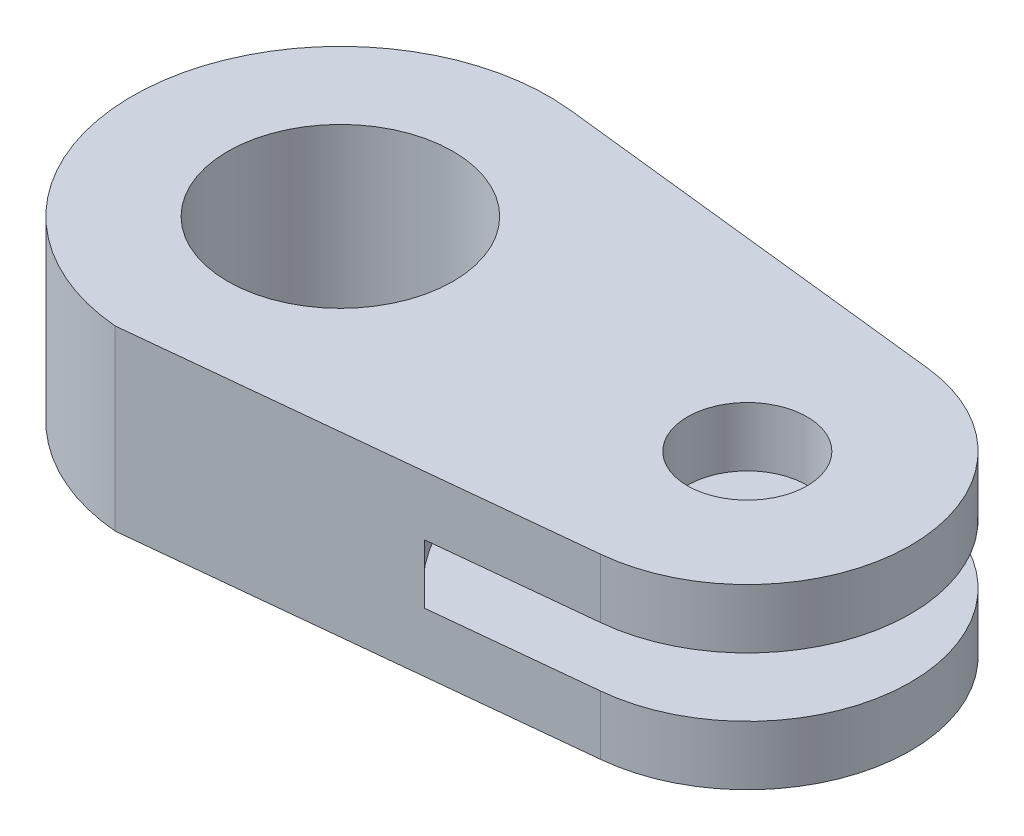
SolidWorks part; units mm, degrees
ref_plane "Front Plane" through (0, 0, 0) normal (0, 0, 1) x (1, 0, 0)
ref_plane "Top Plane" through (0, 0, 0) normal (0, 1, 0) x (1, 0, 0)
ref_plane "Right Plane" through (0, 0, 0) normal (1, 0, 0) x (0, 0, -1)
sketch "Эскиз1" plane through (0, 0, 0) normal (0, 1, 0) x (1, 0, 0)
  line L0 (6.2273, 55.9019) -> (114.7926, 43.8081)
  line L1 (-4.7951, -56.0429) -> (114.102, -43.8795)
  line L2 (0, 0) -> (109.9125, 0) construction
  circle A0 centre (0, 0) radius 30.429
  arc A1 (114.7926, 43.8081) -> (114.102, -43.8795) centre (109.9125, 0) cw
  arc A2 (6.2273, 55.9019) -> (-4.7951, -56.0429) centre (0, 0) ccw
  circle A3 centre (109.9125, 0) radius 16.1558
  point P9 (-4.7951, -56.0429)
extrude "Бобышка-Вытянуть2" add sketch "Эскиз1" along normal mid plane 48
sketch "Эскиз2" plane through (0, 0, 0) normal (0, 1, 0) x (1, 0, 0)
  circle A0 centre (109.9125, 0) radius 62
  dimension "D1" = 124
extrude "Вырез-Вытянуть1" cut sketch "Эскиз2" against normal mid plane 16 contours A0
